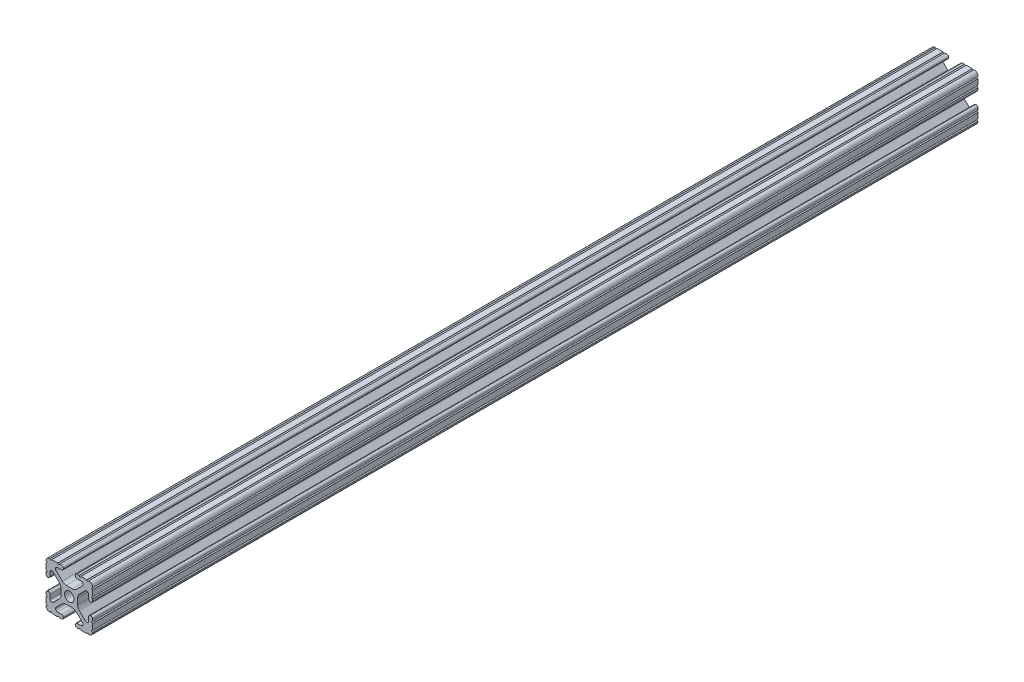
SolidWorks part; units mm, degrees
ref_plane "Front Plane" through (0, 0, 0) normal (0, 0, 1) x (1, 0, 0)
ref_plane "Top Plane" through (0, 0, 0) normal (0, 1, 0) x (1, 0, 0)
ref_plane "Right Plane" through (0, 0, 0) normal (1, 0, 0) x (0, 0, -1)
sketch "Sketch1" plane through (0, 0, 0) normal (0, 0, 1) x (1, 0, 0)
  line L88 (-7.1797, -8.6452) -> (-3.9523, -5.4237)
  line L89 (-1.7093, -4.4958) -> (1.7093, -4.4958)
  line L90 (3.9523, -5.4237) -> (7.1797, -8.6452)
  line L91 (6.4164, -10.4902) -> (4.2875, -10.4902)
  line L92 (3.2385, -11.5392) -> (3.2385, -11.651)
  line L93 (4.2875, -12.7) -> (5.3171, -12.7)
  line L94 (6.3331, -12.7) -> (9.5504, -12.7)
  line L95 (12.7, -9.5504) -> (12.7, -6.3331)
  line L96 (12.7, -5.3171) -> (12.7, -4.2875)
  line L97 (11.651, -3.2385) -> (11.5392, -3.2385)
  line L98 (10.4902, -4.2875) -> (10.4902, -6.4021)
  line L99 (8.7371, -7.1294) -> (5.441, -3.8408)
  line L100 (4.5085, -1.5932) -> (4.5085, 1.5932)
  line L101 (5.441, 3.8408) -> (8.7371, 7.1294)
  line L102 (10.4902, 6.4021) -> (10.4902, 4.2875)
  line L103 (11.5392, 3.2385) -> (11.651, 3.2385)
  line L104 (12.7, 4.2875) -> (12.7, 5.3171)
  line L105 (12.7, 6.3331) -> (12.7, 9.5504)
  line L106 (9.5504, 12.7) -> (6.3331, 12.7)
  line L107 (5.3171, 12.7) -> (4.2875, 12.7)
  line L108 (3.2385, 11.651) -> (3.2385, 11.5392)
  line L109 (4.2875, 10.4902) -> (6.4768, 10.4902)
  line L110 (7.207, 8.7244) -> (3.8983, 5.4232)
  line L111 (1.6558, 4.4958) -> (-1.6558, 4.4958)
  line L112 (-3.8983, 5.4232) -> (-7.207, 8.7244)
  line L113 (-6.4768, 10.4902) -> (-4.2875, 10.4902)
  line L114 (-3.2385, 11.5392) -> (-3.2385, 11.651)
  line L115 (-4.2875, 12.7) -> (-5.3171, 12.7)
  line L116 (-6.3331, 12.7) -> (-9.5504, 12.7)
  line L117 (-12.7, 9.5504) -> (-12.7, 6.3331)
  line L118 (-12.7, 5.3171) -> (-12.7, 4.2875)
  line L119 (-11.651, 3.2385) -> (-11.5392, 3.2385)
  line L120 (-10.4902, 4.2875) -> (-10.4902, 6.4021)
  line L121 (-8.7371, 7.1294) -> (-5.441, 3.8408)
  line L122 (-4.5085, 1.5932) -> (-4.5085, -1.5932)
  line L123 (-5.441, -3.8408) -> (-8.7371, -7.1294)
  line L124 (-10.4902, -6.4021) -> (-10.4902, -4.2875)
  line L125 (-11.5392, -3.2385) -> (-11.651, -3.2385)
  line L126 (-12.7, -4.2875) -> (-12.7, -5.3171)
  line L127 (-12.7, -6.3331) -> (-12.7, -9.5504)
  line L128 (-9.5504, -12.7) -> (-6.3331, -12.7)
  line L129 (-5.3171, -12.7) -> (-4.2875, -12.7)
  line L130 (-3.2385, -11.651) -> (-3.2385, -11.5392)
  line L131 (-4.2875, -10.4902) -> (-6.4164, -10.4902)
  circle A1 centre (0, 0) radius 2.6035
  arc A104 (-7.1797, -8.6452) -> (-6.4164, -10.4902) centre (-6.4164, -9.4098) ccw
  arc A105 (-1.7093, -4.4958) -> (-3.9523, -5.4237) centre (-1.7093, -7.6708) ccw
  arc A106 (3.9523, -5.4237) -> (1.7093, -4.4958) centre (1.7093, -7.6708) ccw
  arc A107 (6.4164, -10.4902) -> (7.1797, -8.6452) centre (6.4164, -9.4098) ccw
  arc A108 (4.2875, -10.4902) -> (3.2385, -11.5392) centre (4.2875, -11.5392) ccw
  arc A109 (3.2385, -11.651) -> (4.2875, -12.7) centre (4.2875, -11.651) ccw
  arc A110 (6.3331, -12.7) -> (5.3171, -12.7) centre (5.8251, -12.7) ccw
  arc A111 (10.5664, -12.6998) -> (9.5504, -12.7) centre (10.0584, -12.7) ccw
  arc A112 (10.5664, -12.6998) -> (12.6998, -10.5664) centre (10.5918, -10.5918) ccw
  arc A113 (12.7, -9.5504) -> (12.6998, -10.5664) centre (12.7, -10.0584) ccw
  arc A114 (12.7, -5.3171) -> (12.7, -6.3331) centre (12.7, -5.8251) ccw
  arc A115 (12.7, -4.2875) -> (11.651, -3.2385) centre (11.651, -4.2875) ccw
  arc A116 (11.5392, -3.2385) -> (10.4902, -4.2875) centre (11.5392, -4.2875) ccw
  arc A117 (8.7371, -7.1294) -> (10.4902, -6.4021) centre (9.4628, -6.4021) ccw
  arc A118 (4.5085, -1.5932) -> (5.441, -3.8408) centre (7.6835, -1.5932) ccw
  arc A119 (5.441, 3.8408) -> (4.5085, 1.5932) centre (7.6835, 1.5932) ccw
  arc A120 (10.4902, 6.4021) -> (8.7371, 7.1294) centre (9.4628, 6.4021) ccw
  arc A121 (10.4902, 4.2875) -> (11.5392, 3.2385) centre (11.5392, 4.2875) ccw
  arc A122 (11.651, 3.2385) -> (12.7, 4.2875) centre (11.651, 4.2875) ccw
  arc A123 (12.7, 6.3331) -> (12.7, 5.3171) centre (12.7, 5.8251) ccw
  arc A124 (12.6998, 10.5664) -> (12.7, 9.5504) centre (12.7, 10.0584) ccw
  arc A125 (12.6998, 10.5664) -> (10.5664, 12.6998) centre (10.5918, 10.5918) ccw
  arc A126 (9.5504, 12.7) -> (10.5664, 12.6998) centre (10.0584, 12.7) ccw
  arc A127 (5.3171, 12.7) -> (6.3331, 12.7) centre (5.8251, 12.7) ccw
  arc A128 (4.2875, 12.7) -> (3.2385, 11.651) centre (4.2875, 11.651) ccw
  arc A129 (3.2385, 11.5392) -> (4.2875, 10.4902) centre (4.2875, 11.5392) ccw
  arc A130 (7.207, 8.7244) -> (6.4768, 10.4902) centre (6.4768, 9.4563) ccw
  arc A131 (1.6558, 4.4958) -> (3.8983, 5.4232) centre (1.6558, 7.6708) ccw
  arc A132 (-3.8983, 5.4232) -> (-1.6558, 4.4958) centre (-1.6558, 7.6708) ccw
  arc A133 (-6.4768, 10.4902) -> (-7.207, 8.7244) centre (-6.4768, 9.4563) ccw
  arc A134 (-4.2875, 10.4902) -> (-3.2385, 11.5392) centre (-4.2875, 11.5392) ccw
  arc A135 (-3.2385, 11.651) -> (-4.2875, 12.7) centre (-4.2875, 11.651) ccw
  arc A136 (-6.3331, 12.7) -> (-5.3171, 12.7) centre (-5.8251, 12.7) ccw
  arc A137 (-10.5664, 12.6998) -> (-9.5504, 12.7) centre (-10.0584, 12.7) ccw
  arc A138 (-10.5664, 12.6998) -> (-12.6998, 10.5664) centre (-10.5918, 10.5918) ccw
  arc A139 (-12.7, 9.5504) -> (-12.6998, 10.5664) centre (-12.7, 10.0584) ccw
  arc A140 (-12.7, 5.3171) -> (-12.7, 6.3331) centre (-12.7, 5.8251) ccw
  arc A141 (-12.7, 4.2875) -> (-11.651, 3.2385) centre (-11.651, 4.2875) ccw
  arc A142 (-11.5392, 3.2385) -> (-10.4902, 4.2875) centre (-11.5392, 4.2875) ccw
  arc A143 (-8.7371, 7.1294) -> (-10.4902, 6.4021) centre (-9.4628, 6.4021) ccw
  arc A144 (-4.5085, 1.5932) -> (-5.441, 3.8408) centre (-7.6835, 1.5932) ccw
  arc A145 (-5.441, -3.8408) -> (-4.5085, -1.5932) centre (-7.6835, -1.5932) ccw
  arc A146 (-10.4902, -6.4021) -> (-8.7371, -7.1294) centre (-9.4628, -6.4021) ccw
  arc A147 (-10.4902, -4.2875) -> (-11.5392, -3.2385) centre (-11.5392, -4.2875) ccw
  arc A148 (-11.651, -3.2385) -> (-12.7, -4.2875) centre (-11.651, -4.2875) ccw
  arc A149 (-12.7, -6.3331) -> (-12.7, -5.3171) centre (-12.7, -5.8251) ccw
  arc A150 (-12.6998, -10.5664) -> (-12.7, -9.5504) centre (-12.7, -10.0584) ccw
  arc A151 (-12.6998, -10.5664) -> (-10.5664, -12.6998) centre (-10.5918, -10.5918) ccw
  arc A152 (-9.5504, -12.7) -> (-10.5664, -12.6998) centre (-10.0584, -12.7) ccw
  arc A153 (-5.3171, -12.7) -> (-6.3331, -12.7) centre (-5.8251, -12.7) ccw
  arc A154 (-4.2875, -12.7) -> (-3.2385, -11.651) centre (-4.2875, -11.651) ccw
  arc A155 (-3.2385, -11.5392) -> (-4.2875, -10.4902) centre (-4.2875, -11.5392) ccw
extrude "Boss-Extrude1" add sketch "Sketch1" along normal mid plane 482.6
